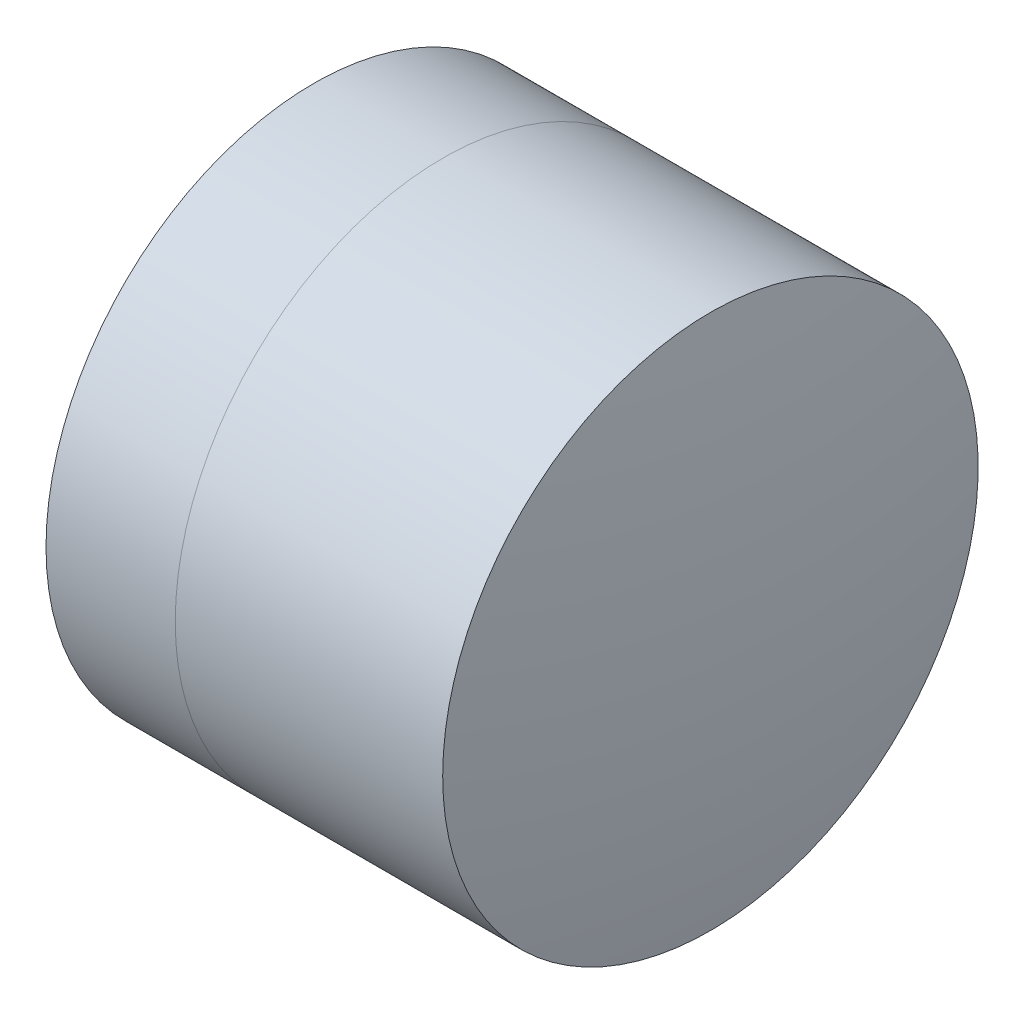
SolidWorks part; units mm, degrees
ref_plane "前视基准面" through (0, 0, 0) normal (0, 0, 1) x (1, 0, 0)
ref_plane "上视基准面" through (0, 0, 0) normal (0, 1, 0) x (1, 0, 0)
ref_plane "右视基准面" through (0, 0, 0) normal (1, 0, 0) x (0, 0, -1)
sketch "草图1" plane through (0, 0, 0) normal (0, 1, 0) x (1, 0, 0)
  line L0 (-0.8161, 0) -> (5.2377, 0) construction
  line L1 (2.47, -2.5) -> (3.6768, -2.5)
  line L2 (2.47, 2.5) -> (3.6768, 2.5)
  arc A0 (3.6768, -2.5) -> (3.6768, 2.5) centre (0.1782, 0) ccw
  arc A1 (2.47, 2.5) -> (2.47, -2.5) centre (8.5782, 0) ccw
  point P10 (1.9782, 0)
  point P11 (4.4782, 0)
  dimension "D3" = 6.6
  dimension "D4" = 4.3
  dimension "D1" = 2.5
  dimension "D2" = 2.5
  dimension "D5" = 2.5
revolve "旋转1" add sketch "草图1" angle 360 about L0
sketch "草图2" plane through (0, 0, 0) normal (0, 1, 0) x (1, 0, 0)
  line L0 (-0.5519, 0) -> (6.7463, 0) construction
  line L2 (3.6768, 2.5) -> (6.1739, 2.5)
  line L3 (3.6768, -2.5) -> (6.1739, -2.5)
  arc A0 (6.1739, -2.5) -> (6.1739, 2.5) centre (-9.0218, 0) ccw
  arc A1 (3.6768, -2.5) -> (3.6768, 2.5) centre (0.1782, 0) ccw construction
  arc A2 (3.6768, -2.5) -> (3.6768, 2.5) centre (0.1782, 0) ccw
  point P4 (4.4782, 0)
  point P8 (6.3782, 0)
  point P9 (6.7463, 0)
  dimension "D1" = 15.4
  dimension "D2" = 1.9
revolve "旋转3" add sketch "草图2" angle 360 about L0
